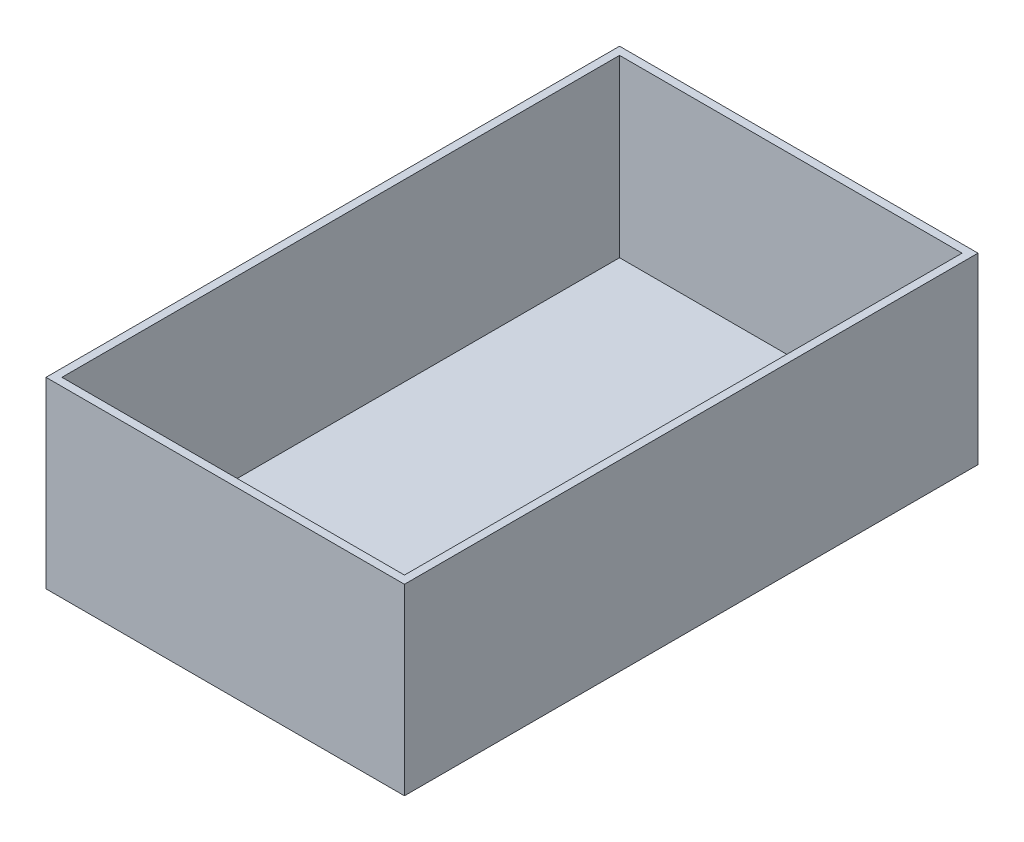
SolidWorks part; units mm, degrees
material "Acrylic (Medium-high impact)"
ref_plane "Front Plane" through (0, 0, 0) normal (0, 0, 1) x (1, 0, 0)
ref_plane "Top Plane" through (0, 0, 0) normal (0, 1, 0) x (1, 0, 0)
ref_plane "Right Plane" through (0, 0, 0) normal (1, 0, 0) x (0, 0, -1)
sketch "Sketch1" plane through (0, 0, 0) normal (0, 1, 0) x (1, 0, 0)
  line L1 (-53.5487, 74.4134) -> (82.9763, 74.4134)
  line L2 (-53.5487, 74.4134) -> (-53.5487, -147.8366)
  line L3 (-53.5487, -147.8366) -> (82.9763, -147.8366)
  line L4 (82.9763, 74.4134) -> (82.9763, -147.8366)
  dimension "D1" = 136.525
  dimension "D2" = 222.25
extrude "Boss-Extrude1" add sketch "Sketch1" along normal blind 69.85
shell "Shell1" thickness 3.175
